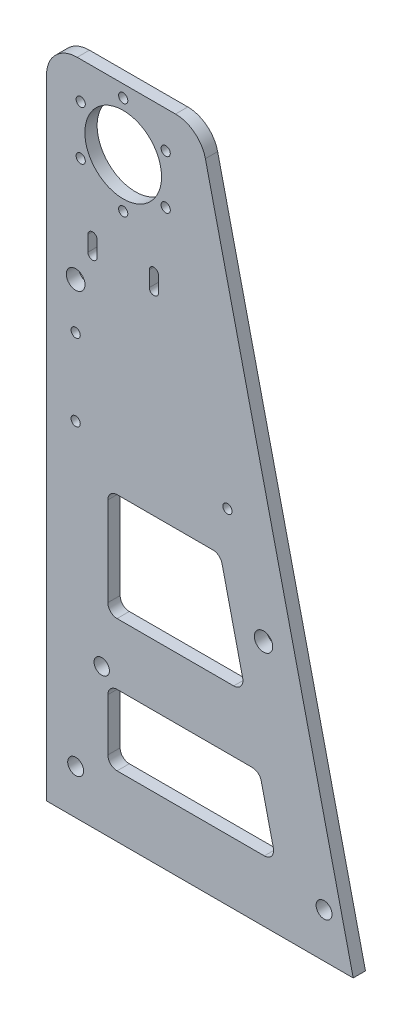
SolidWorks part; units mm, degrees
material "Gerais  - 6061-T6"
ref_plane "Plano frontal" through (0, 0, 0) normal (0, 0, 1) x (1, 0, 0)
ref_plane "Plano superior" through (0, 0, 0) normal (0, 1, 0) x (1, 0, 0)
ref_plane "Plano direito" through (0, 0, 0) normal (1, 0, 0) x (0, 0, -1)
sketch "Esboço1" plane through (0, 0, 0) normal (0, 0, 1) x (1, 0, 0)
  line L0 (0, 0) -> (0, 215)
  line L2 (100, 0) -> (0, 0)
  line L3 (0, 215) -> (50, 215)
  line L4 (50, 215) -> (100, 0)
  line L5 (10, 75.4302) -> (10, 15) construction
  line L6 (25, 215) -> (25, 175) construction
  line L7 (10, 15) -> (85.7122, 15) construction
  line L8 (85.7122, 15) -> (71.6586, 75.4302) construction
  line L9 (71.6586, 75.4302) -> (10, 75.4302) construction
  line L10 (20, 95) -> (20, 66)
  line L11 (23, 63) -> (61.0374, 63)
  line L12 (63.9594, 66.6795) -> (57.2152, 95.6795)
  line L13 (54.2932, 98) -> (23, 98)
  line L14 (20, 40) -> (20, 23)
  line L15 (23, 20) -> (71.0374, 20)
  line L16 (73.9594, 23.6795) -> (70.0059, 40.6795)
  line L17 (23, 43) -> (67.0839, 43)
  circle A0 centre (25, 195) radius 12.5
  circle A1 centre (25, 195) radius 16 construction
  circle A2 centre (25, 211) radius 1.5
  arc A8 (70.0059, 40.6795) -> (67.0839, 43) centre (67.0839, 40) ccw
  arc A9 (71.0374, 20) -> (73.9594, 23.6795) centre (71.0374, 23) ccw
  arc A10 (20, 23) -> (23, 20) centre (23, 23) ccw
  arc A11 (20, 40) -> (23, 43) centre (23, 40) cw
  arc A12 (57.2152, 95.6795) -> (54.2932, 98) centre (54.2932, 95) ccw
  arc A13 (61.0374, 63) -> (63.9594, 66.6795) centre (61.0374, 66) ccw
  arc A14 (20, 66) -> (23, 63) centre (23, 66) ccw
  arc A15 (20, 95) -> (23, 98) centre (23, 95) cw
  circle A16 centre (38.8564, 203) radius 1.5
  circle A17 centre (38.8564, 187) radius 1.5
  circle A18 centre (25, 179) radius 1.5
  circle A19 centre (11.1436, 187) radius 1.5
  circle A20 centre (11.1436, 203) radius 1.5
  circle A21 centre (18, 47) radius 2.5
  point P26 (22.5, 105)
  point P49 (20, 63)
  point P55 (25, 175)
  point P56 (25, 195)
  dimension "D3" = 20
  dimension "D4" = 25
  dimension "D6" = 32
  dimension "D7" = 3
  dimension "D21" = 3
  dimension "D15" = 18
  dimension "D16" = 47
  dimension "D17" = 5
  dimension "D1" = 215
  dimension "D2" = 100
  dimension "D5" = 50
  dimension "D9" = 25
  dimension "D10" = 6
  dimension "D11" = 20
  dimension "D12" = 20
  dimension "D13" = 15
  dimension "D14" = 20
  dimension "D18" = 10
  dimension "D20" = 20
  dimension "D22" = 23
  dimension "D8" = 35
extrude "Ressalto-extrusão2" add sketch "Esboço1" along normal blind 4
fillet "Filete1" radius 10 2 edges at (0, 215, 2) (50, 215, 2)
sketch "Esboço2" plane through (0, 0, 4) normal (0, 0, 1) x (1, 0, 0)
  line L0 (0, 0) -> (100, 0) construction
  line L1 (0, 205) -> (0, 0) construction
  line L2 (15, 164.21) -> (35, 164.21) construction
  line L3 (15, 161.71) -> (15, 166.71) construction
  line L4 (13.5, 161.71) -> (13.5, 166.71)
  line L5 (16.5, 161.71) -> (16.5, 166.71)
  line L6 (35, 161.71) -> (35, 166.71) construction
  line L7 (33.5, 161.71) -> (33.5, 166.71)
  line L8 (36.5, 161.71) -> (36.5, 166.71)
  circle A0 centre (9.5, 137) radius 1.5
  circle A1 centre (90.5, 14.5) radius 2.6
  circle A2 centre (9.5, 112) radius 1.5
  circle A3 centre (9.5, 152) radius 3.05
  circle A4 centre (15, 164.21) radius 1.5 construction
  circle A5 centre (35, 164.21) radius 1.5 construction
  arc A6 (13.5, 161.71) -> (16.5, 161.71) centre (15, 161.71) ccw
  arc A7 (16.5, 166.71) -> (13.5, 166.71) centre (15, 166.71) ccw
  arc A8 (33.5, 161.71) -> (36.5, 161.71) centre (35, 161.71) ccw
  arc A9 (36.5, 166.71) -> (33.5, 166.71) centre (35, 166.71) ccw
  circle A10 centre (59, 112) radius 1.5
  circle A11 centre (9.5, 14.5) radius 2.6
  point P2 (9.5, 112)
  point P3 (9.5, 137)
  point P18 (25, 195)
  point P20 (25, 164.21)
  point P22 (15, 164.21)
  point P30 (35, 164.21)
  dimension "D4" = 3
  dimension "D7" = 5.2
  dimension "D8" = 6.1
  dimension "D10" = 3
  dimension "D14" = 49.5
  dimension "D15" = 9.5
  dimension "D1" = 112
  dimension "D2" = 25
  dimension "D3" = 9.5
  dimension "D5" = 14.5
  dimension "D6" = 9.5
  dimension "D9" = 15
  dimension "D11" = 20
  dimension "D12" = 30.79
  dimension "D13" = 5
extrude "Corte-extrusão1" cut sketch "Esboço2" against normal through all
sketch "Esboço3" plane through (0, 0, 4) normal (0, 0, 1) x (1, 0, 0)
  circle A1 centre (70.7598, 80.3986) radius 3
extrude "Corte-extrusão2" cut sketch "Esboço3" against normal through all
